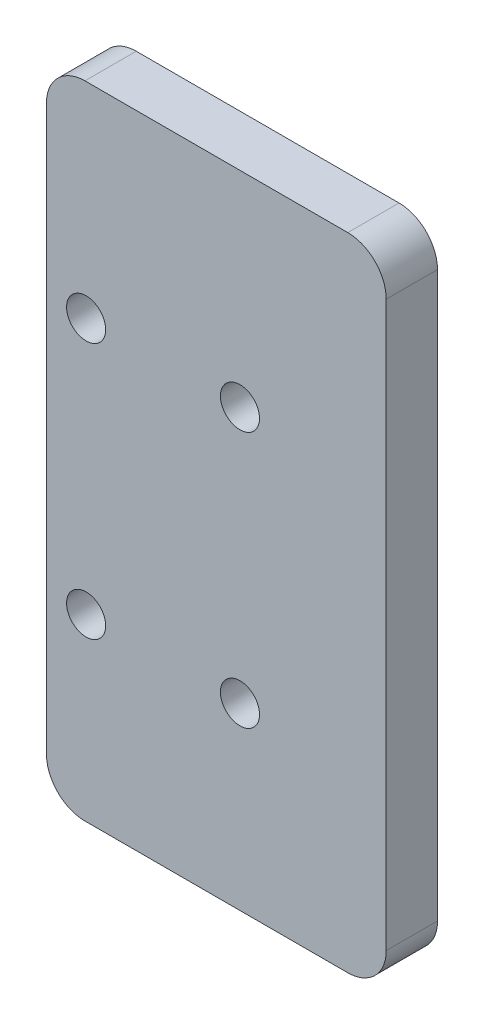
SolidWorks part; units mm, degrees
material "Thornel Mat VMA"
ref_plane "前视基准面" through (0, 0, 0) normal (0, 0, 1) x (1, 0, 0)
ref_plane "上视基准面" through (0, 0, 0) normal (0, 1, 0) x (1, 0, 0)
ref_plane "右视基准面" through (0, 0, 0) normal (1, 0, 0) x (0, 0, -1)
other "Configuration Table"
sketch "草图1" plane through (0, 0, 0) normal (0, 0, 1) x (1, 0, 0)
  line L1 (-13.25, -25) -> (13.25, -25)
  line L2 (-13.25, -25) -> (-13.25, 25)
  line L3 (-13.25, 25) -> (13.25, 25)
  line L4 (13.25, -25) -> (13.25, 25)
  line L5 (-13.25, -25) -> (13.25, 25) construction
  line L6 (-13.25, 25) -> (13.25, -25) construction
  point P0 (0, 0)
  dimension "D1" = 26.5
  dimension "D2" = 50
extrude "凸台-拉伸1" add sketch "草图1" along normal blind 4
sketch "草图2" plane through (0, 0, 4) normal (0, 0, 1) x (1, 0, 0)
  circle A4 centre (-10.1586, 9) radius 1.525
  circle A5 centre (1.8414, 9) radius 1.525
  circle A6 centre (-10.1586, -11) radius 1.525
  circle A7 centre (1.8414, -11) radius 1.525
  circle A8 centre (-10.1586, 9) radius 1.25 construction
  circle A9 centre (-10.1586, -11) radius 1.25 construction
  circle A10 centre (1.8414, -11) radius 1.25 construction
  circle A11 centre (1.8414, 9) radius 1.25 construction
  dimension "D1" = 3.05
extrude "切除-拉伸1" cut sketch "草图2" against normal blind 4
fillet "圆角1" radius 3 4 edges at (13.25, -25, 2) (-13.25, -25, 2) (-13.25, 25, 2) (13.25, 25, 2)
